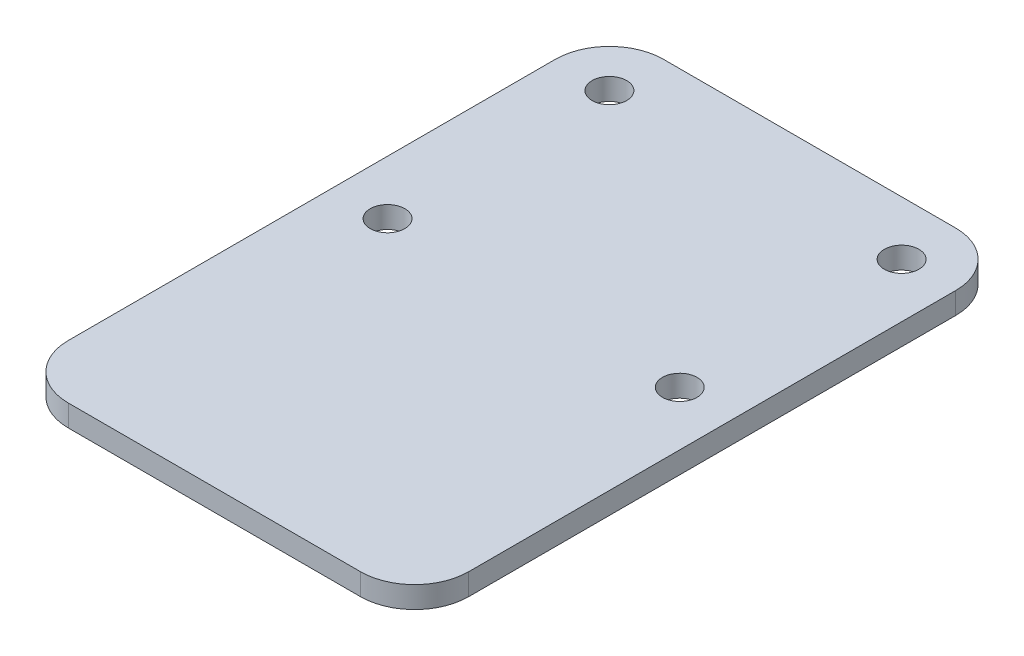
SolidWorks part; units mm, degrees
other "Cámara1"
material "PET"
ref_plane "Alzado" through (0, 0, 0) normal (0, 0, 1) x (1, 0, 0)
ref_plane "Planta" through (0, 0, 0) normal (0, 1, 0) x (1, 0, 0)
ref_plane "Vista lateral" through (0, 0, 0) normal (1, 0, 0) x (0, 0, -1)
sketch "Croquis1" plane through (0, 0, 0) normal (0, 1, 0) x (1, 0, 0)
  line L0 (0, -60.9945) -> (0, 60.9945) construction
  line L1 (-18.5, -27.5) -> (18.5, -27.5)
  line L2 (-18.5, -27.5) -> (-18.5, 27.5)
  line L3 (-18.5, 27.5) -> (18.5, 27.5)
  line L4 (18.5, -27.5) -> (18.5, 27.5)
  line L5 (-18.5, -27.5) -> (18.5, 27.5) construction
  line L6 (-18.5, 27.5) -> (18.5, -27.5) construction
  circle A0 centre (-13.5, 22.5) radius 1.6
  circle A1 centre (-13.5, 2) radius 1.6
  circle A2 centre (13.5, 2) radius 1.6
  circle A3 centre (13.5, 22.5) radius 1.6
  point P0 (0, 0)
  point P13 (0, 0)
  dimension "D1" = 3.2
  dimension "D4" = 5
  dimension "D6" = 5
  dimension "D2" = 13.5
  dimension "D3" = 20.5
  dimension "D5" = 55
extrude "Saliente-Extruir1" add sketch "Croquis1" along normal blind 2
fillet "Redondeo1" radius 5 4 edges at (18.5, 1, -27.5) (-18.5, 1, -27.5) (-18.5, 1, 27.5) (18.5, 1, 27.5)
